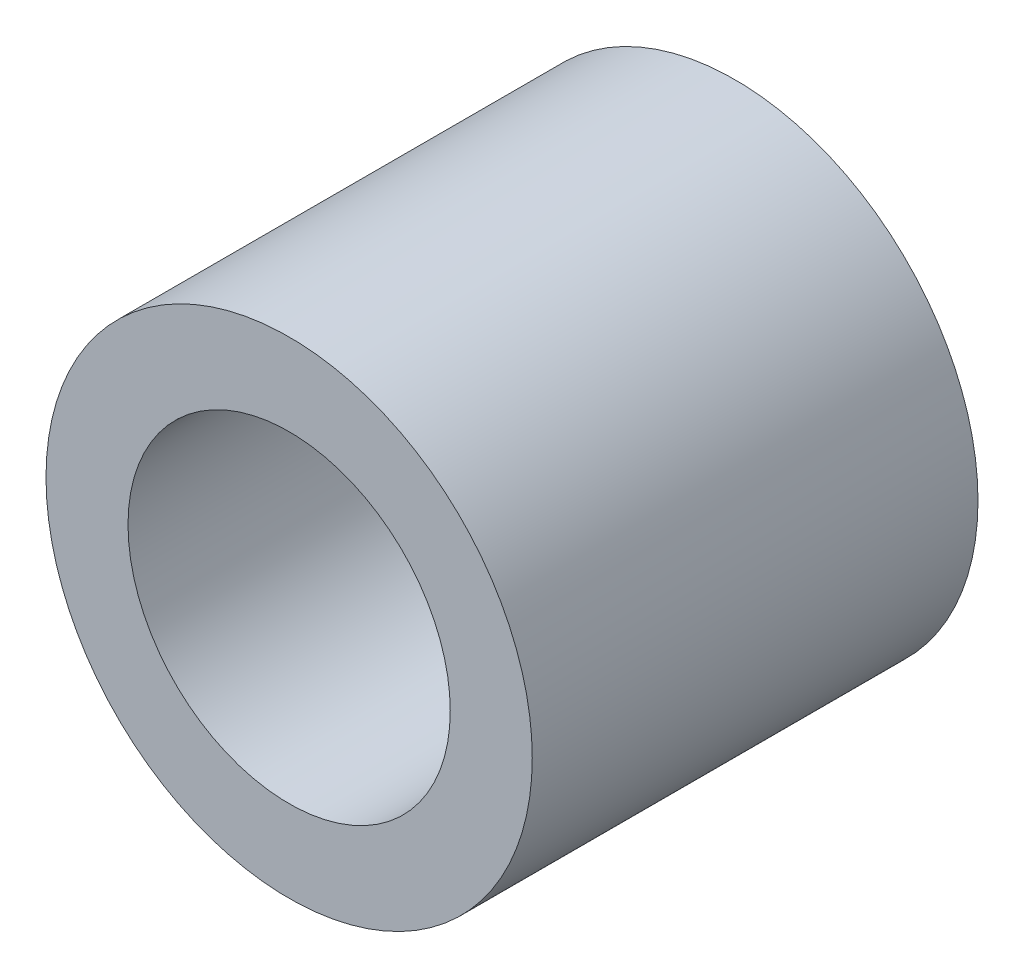
SolidWorks part; units mm, degrees
ref_plane "Front" through (0, 0, 0) normal (0, 0, 1) x (1, 0, 0)
ref_plane "Top" through (0, 0, 0) normal (0, 1, 0) x (1, 0, 0)
ref_plane "Right" through (0, 0, 0) normal (1, 0, 0) x (0, 0, -1)
sketch "Sketch1" plane through (0, 0, 0) normal (0, 0, 1) x (1, 0, 0)
  circle A0 centre (0, 0) radius 3.81
  circle A1 centre (0, 0) radius 2.525
  dimension "D1" = 7.62
  dimension "D2" = 5.05
extrude "Boss-Extrude1" add sketch "Sketch1" along normal blind 6.985
